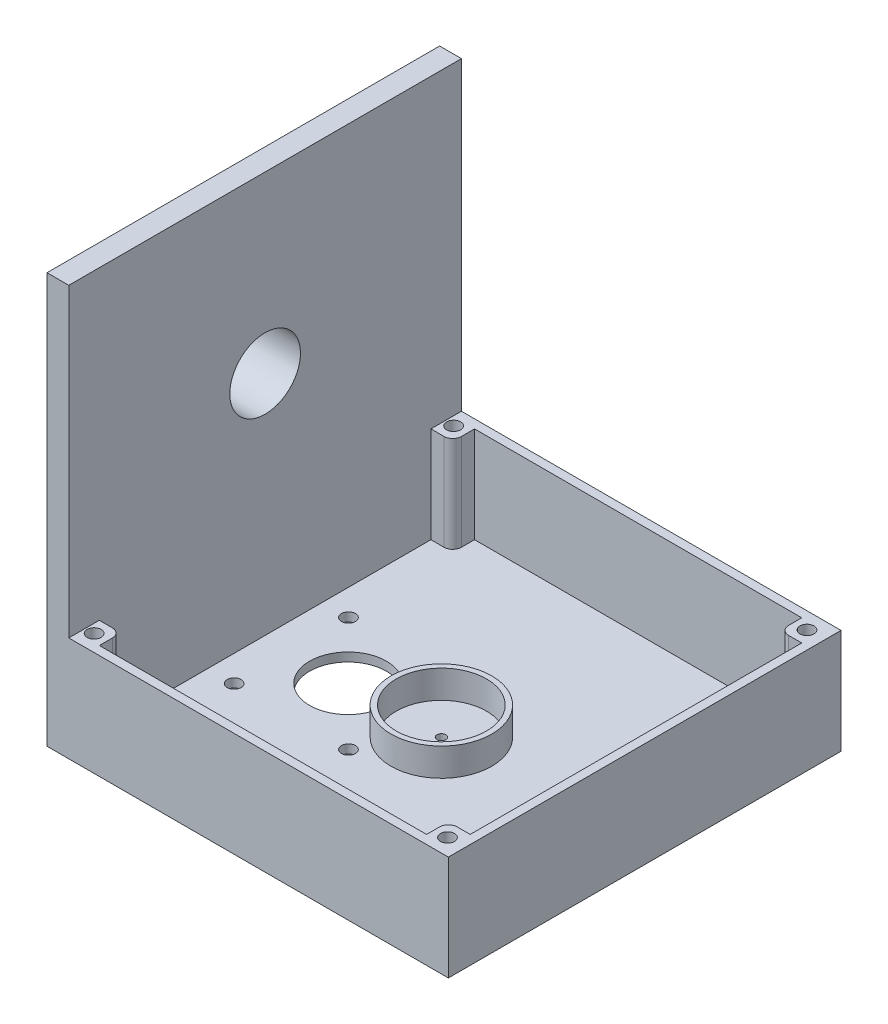
SolidWorks part; units mm, degrees
ref_plane "Front Plane" through (0, 0, 0) normal (0, 0, 1) x (1, 0, 0)
ref_plane "Top Plane" through (0, 0, 0) normal (0, 1, 0) x (1, 0, 0)
ref_plane "Right Plane" through (0, 0, 0) normal (1, 0, 0) x (0, 0, -1)
sketch "Sketch1" plane through (0, 0, 0) normal (0, 0, 1) x (1, 0, 0)
  line L0 (0, 0) -> (0, 88.9)
  line L1 (0, 88.9) -> (-6.35, 88.9)
  line L2 (-6.35, 88.9) -> (-6.35, -30.48)
  line L3 (-6.35, -30.48) -> (110.49, -30.48)
  line L4 (110.49, -30.48) -> (110.49, 0)
  line L5 (110.49, 0) -> (0, 0)
  dimension "D1" = 6.35
  dimension "D2" = 30.48
  dimension "D3" = 88.9
  dimension "D4" = 116.84
extrude "Boss-Extrude1" add sketch "Sketch1" along normal blind 114.3
sketch "Sketch3" plane through (0, 0, 0) normal (0, 1, 0) x (1, 0, 0)
  line L0 (110.49, -114.3) -> (110.49, 0) construction
  line L1 (107.95, -2.54) -> (0, -2.54)
  line L2 (107.95, -2.54) -> (107.95, -111.76)
  line L3 (107.95, -111.76) -> (0, -111.76)
  line L5 (110.49, 0) -> (0, 0) construction
  line L7 (110.49, -114.3) -> (0, -114.3) construction
  line L8 (0, -114.3) -> (0, 0) construction
  line L9 (0, -2.54) -> (0, -111.76)
  dimension "D1" = 2.54
  dimension "D2" = 2.54
  dimension "D4" = 2.54
extrude "Cut-Extrude1" cut sketch "Sketch3" against normal blind 27.94
sketch "Sketch4" plane through (0, 0, 0) normal (0, 1, 0) x (1, 0, 0)
  line L0 (53.975, -2.54) -> (53.975, -10.0889) construction
  line L1 (0, -2.54) -> (6.35, -2.54)
  line L2 (0, -2.54) -> (0, -8.89)
  line L3 (0, -8.89) -> (3.81, -8.89)
  line L4 (6.35, -2.54) -> (6.35, -6.35)
  line L5 (107.95, -2.54) -> (0, -2.54) construction
  line L6 (107.95, -57.15) -> (85.6603, -57.15) construction
  line L7 (110.49, -114.3) -> (0, -114.3) construction
  line L8 (107.95, -111.76) -> (107.95, -2.54) construction
  line L9 (101.6, -2.54) -> (101.6, -6.35)
  line L10 (107.95, -8.89) -> (104.14, -8.89)
  line L11 (107.95, -2.54) -> (107.95, -8.89)
  line L12 (107.95, -2.54) -> (101.6, -2.54)
  line L13 (53.975, -111.76) -> (53.975, -104.2111) construction
  line L14 (107.95, -111.76) -> (101.6, -111.76)
  line L15 (107.95, -111.76) -> (107.95, -105.41)
  line L16 (107.95, -105.41) -> (104.14, -105.41)
  line L17 (101.6, -111.76) -> (101.6, -107.95)
  line L18 (6.35, -111.76) -> (6.35, -107.95)
  line L19 (0, -105.41) -> (3.81, -105.41)
  line L20 (0, -111.76) -> (0, -105.41)
  line L21 (0, -111.76) -> (6.35, -111.76)
  line L22 (110.49, -114.3) -> (110.49, 0) construction
  arc A0 (3.81, -8.89) -> (6.35, -6.35) centre (3.81, -6.35) ccw
  arc A1 (104.14, -8.89) -> (101.6, -6.35) centre (104.14, -6.35) cw
  arc A2 (104.14, -105.41) -> (101.6, -107.95) centre (104.14, -107.95) ccw
  arc A3 (3.81, -105.41) -> (6.35, -107.95) centre (3.81, -107.95) cw
  circle A4 centre (105.41, -109.474) radius 2.032
  circle A5 centre (2.54, -109.474) radius 2.032
  circle A6 centre (2.54, -4.826) radius 2.032
  circle A7 centre (105.41, -4.826) radius 2.032
  dimension "D1" = 2.54
  dimension "D2" = 4.064
  dimension "D5" = 4.826
  dimension "D6" = 5.08
  dimension "D3" = 3.81
  dimension "D4" = 3.81
extrude "Boss-Extrude14" add sketch "Sketch4" against normal up to next
sketch "Sketch5" plane through (0, -30.48, 0) normal (0, -1, 0) x (1, 0, 0)
  line L0 (-6.35, 57.15) -> (8.5207, 57.15) construction
  line L1 (-6.35, 114.3) -> (-6.35, 0) construction
  line L3 (-6.35, 114.3) -> (-6.35, 0) construction
  circle A0 centre (7.62, 73.787) radius 2.032
  circle A1 centre (40.894, 73.787) radius 2.032
  circle A2 centre (40.894, 40.513) radius 2.032
  circle A4 centre (7.62, 40.513) radius 2.032
  circle A5 centre (24.13, 57.15) radius 11.176
  circle A6 centre (51.308, 57.15) radius 1.27
  dimension "D3" = 4.064
  dimension "D4" = 13.97
  dimension "D5" = 16.637
  dimension "D6" = 30.48
  dimension "D7" = 22.352
  dimension "D8" = 2.54
  dimension "D9" = 27.178
  dimension "D1" = 33.274
  dimension "D2" = 33.274
extrude "Cut-Extrude2" cut sketch "Sketch5" against normal blind 2.54
sketch "Sketch7" plane through (-6.35, 0, 0) normal (-1, 0, 0) x (0, 0, 1)
  line L0 (0, 88.9) -> (0, -30.48) construction
  line L1 (114.3, 88.9) -> (0, 88.9) construction
  circle A0 centre (57.15, 38.1) radius 12.319
  dimension "D1" = 57.15
  dimension "D2" = 50.8
  dimension "D3" = 24.638
extrude "Boss-Extrude15" add sketch "Sketch7" along normal blind 24.5
sketch "Sketch8" plane through (-30.85, 0, 0) normal (-1, 0, 0) x (0, 0, 1)
  circle A0 centre (57.15, 38.1) radius 10.287
  circle A1 centre (57.15, 38.1) radius 12.319 construction
  dimension "D1" = 2.032
extrude "Cut-Extrude3" cut sketch "Sketch8" against normal up to next
sketch "Sketch11" plane through (-6.35, 0, 0) normal (-1, 0, 0) x (0, 0, 1)
  line L0 (54.737, 50.1804) -> (54.737, 53.3073)
  line L1 (57.15, 38.1) -> (57.15, 20.8803) construction
  line L2 (54.737, 53.3073) -> (59.563, 53.3073)
  line L3 (59.563, 53.3073) -> (59.563, 50.1804)
  circle A0 centre (57.15, 38.1) radius 12.319 construction
  arc A1 (59.563, 50.1804) -> (54.737, 50.1804) centre (57.15, 38.1) ccw
  point P4 (57.15, 50.419)
  dimension "D1" = 3.1269
  dimension "D2" = 4.826
extrude "Boss-Extrude17" add sketch "Sketch11" along normal blind 5.08
sketch "Sketch13" plane through (-6.35, 0, 0) normal (-1, 0, 0) x (0, 0, 1)
  line L0 (57.15, 38.1) -> (57.15, 121.2119) construction
  circle A0 centre (57.15, -5.842) radius 3.175
  circle A1 centre (57.15, 38.1) radius 10.287 construction
  dimension "D1" = 6.35
  dimension "D2" = 43.942
sketch "Sketch14" plane through (-30.85, 0, 0) normal (-1, 0, 0) x (0, 0, 1)
  circle A1 centre (57.15, 38.1) radius 12.319
  circle A2 centre (57.15, 38.1) radius 12.319
  dimension "D1" = 0
extrude "Cut-Extrude4" [suppressed] cut sketch "Sketch14" against normal through all flip side to cut
sketch "Sketch15" plane through (0, 0, 0) normal (0, 0, 1) x (1, 0, 0)
  line L1 (-18.7589, 68.2287) -> (-13.6789, 68.2287)
  line L2 (-18.7589, 68.2287) -> (-18.7589, 15.1711)
  line L3 (-18.7589, 15.1711) -> (-13.6789, 15.1711)
  line L4 (-13.6789, 68.2287) -> (-13.6789, 15.1711)
  dimension "D1" = 5.08
extrude "Cut-Extrude5" [suppressed] cut sketch "Sketch15" along normal through all flip side to cut
sketch "Sketch16" plane through (0, -27.94, 0) normal (0, 1, 0) x (1, 0, 0)
  circle A0 centre (51.308, -57.15) radius 14.6685
  circle A1 centre (51.308, -57.15) radius 13.1445
  dimension "D1" = 26.289
  dimension "D2" = 1.524
extrude "Boss-Extrude18" add sketch "Sketch16" along normal blind 8.128
